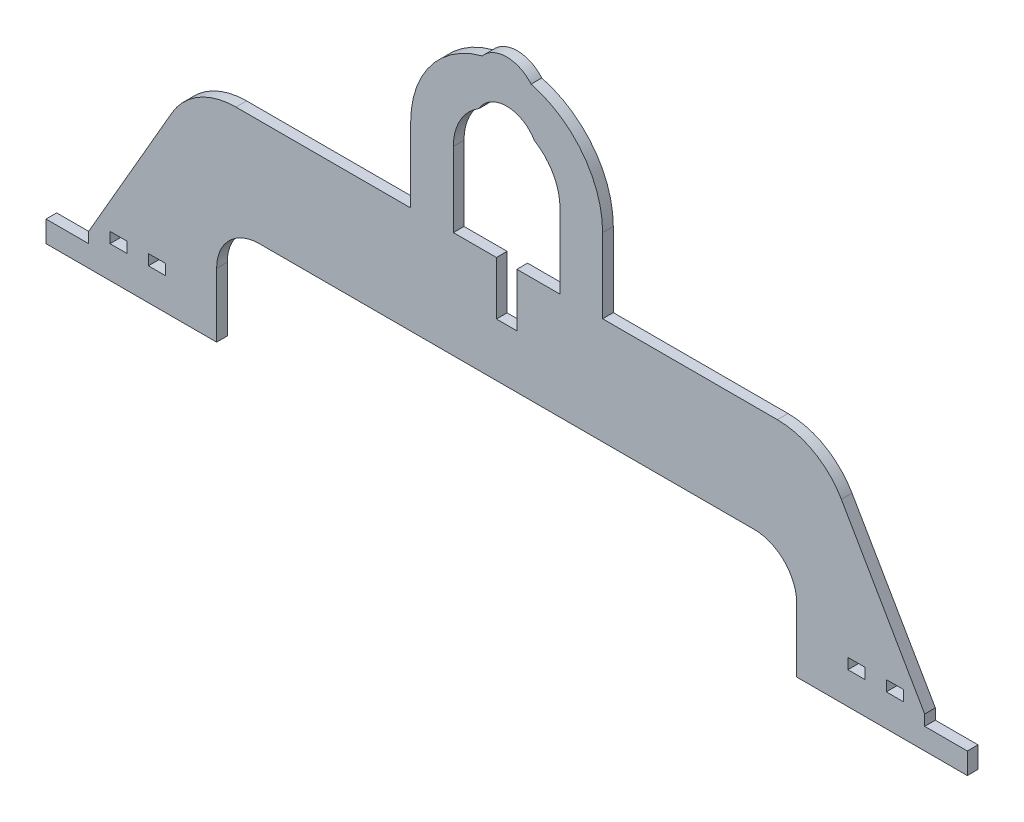
SolidWorks part; units mm, degrees
ref_plane "前视基准面" through (0, 0, 0) normal (0, 0, 1) x (1, 0, 0)
ref_plane "上视基准面" through (0, 0, 0) normal (0, 1, 0) x (1, 0, 0)
ref_plane "右视基准面" through (0, 0, 0) normal (1, 0, 0) x (0, 0, -1)
sketch "草图1" plane through (0, 0, 0) normal (0, 0, 1) x (1, 0, 0)
  line L12 (0, 256.6802) -> (0, -57.0056) construction
  line L13 (-216, 0) -> (-216, 10)
  line L14 (-216, 10) -> (-196, 10)
  line L15 (-196, 10) -> (-196, 15)
  line L17 (-196, 15) -> (-146.9252, 100)
  line L18 (-146.9252, 100) -> (146.9252, 100)
  line L20 (136, 50) -> (-136, 50)
  line L21 (-136, 50) -> (-136, 0)
  line L22 (-136, 0) -> (-216, 0)
  line L23 (136, 50) -> (136, 0)
  line L24 (136, 0) -> (216, 0)
  line L25 (216, 0) -> (216, 10)
  line L26 (216, 10) -> (196, 10)
  line L27 (196, 10) -> (196, 15)
  line L29 (196, 15) -> (146.9252, 100)
  point P5 (0, 0)
  point P8 (0, 256.6802)
  dimension "D1" = 10
  dimension "D2" = 5
  dimension "D3" = 20
  dimension "D4" = 50
  dimension "D5" = 392
  dimension "D6" = 80
  dimension "D7" = 100
  dimension "D8" = 60
extrude "凸台-拉伸1" add sketch "草图1" along normal blind 5
sketch "草图2" plane through (0, 0, 5) normal (0, 0, 1) x (1, 0, 0)
  line L0 (-146.9252, 100) -> (-126.9252, 100)
  line L1 (146.9252, 100) -> (-146.9252, 100) construction
  line L2 (-146.9252, 100) -> (-156.9252, 82.6795)
  line L3 (-146.9252, 100) -> (-196, 15) construction
  line L4 (0, 114.8473) -> (0, -48.9602) construction
  line L5 (146.9252, 100) -> (156.9252, 82.6795)
  line L6 (146.9252, 100) -> (126.9252, 100)
  arc A0 (-126.9252, 100) -> (-156.9252, 82.6795) centre (-126.9252, 65.359) ccw
  arc A1 (126.9252, 100) -> (156.9252, 82.6795) centre (126.9252, 65.359) cw
  dimension "D1" = 20
extrude "切除-拉伸1" cut sketch "草图2" against normal up to next
sketch "草图3" plane through (0, 0, 5) normal (0, 0, 1) x (1, 0, 0)
  line L0 (-116, 50) -> (-136, 50)
  line L1 (-136, 50) -> (136, 50) construction
  line L2 (-136, 50) -> (-136, 30)
  line L3 (-136, 0) -> (-136, 50) construction
  line L4 (0, 39.1826) -> (0, -70.8264) construction
  line L5 (136, 50) -> (136, 30)
  line L6 (116, 50) -> (136, 50)
  arc A0 (-116, 50) -> (-136, 30) centre (-116, 30) ccw
  arc A1 (116, 50) -> (136, 30) centre (116, 30) cw
  dimension "D1" = 20
extrude "凸台-拉伸2" add sketch "草图3" against normal up to surface (5 mm away) up to face at (0, 33.9623, 0)
sketch "草图4" plane through (0, 0, 5) normal (0, 0, 1) x (1, 0, 0)
  line L0 (126.9252, 100) -> (-126.9252, 100) construction
  line L1 (-4.8, 75) -> (4.8, 75)
  line L2 (-4.8, 75) -> (-4.8, 125)
  line L3 (-4.8, 125) -> (4.8, 125)
  line L4 (4.8, 75) -> (4.8, 125)
  line L5 (-4.8, 75) -> (4.8, 125) construction
  line L6 (-4.8, 125) -> (4.8, 75) construction
  point P0 (0, 100)
  dimension "D1" = 9.6
  dimension "D2" = 25
extrude "切除-拉伸2" cut sketch "草图4" against normal up to next
sketch "草图5" plane through (0, 0, 0) normal (0, 0, -1) x (-1, 0, 0)
  line L0 (45, 100) -> (45, 135)
  line L1 (4.8, 100) -> (126.9252, 100) construction
  line L2 (45, 100) -> (25, 100)
  line L3 (25, 100) -> (25, 135)
  line L4 (-25, 135) -> (-25, 100)
  line L5 (-126.9252, 100) -> (-4.8, 100) construction
  line L6 (-25, 100) -> (-45, 100)
  line L7 (-45, 100) -> (-45, 135)
  arc A0 (25, 135) -> (12.973, 156.3706) centre (0, 135) ccw
  arc A1 (45, 135) -> (11.4627, 178.5156) centre (0, 135) ccw
  arc A2 (12.973, 156.3706) -> (-12.973, 156.3706) centre (0, 148.8405) ccw
  arc A3 (11.4627, 178.5156) -> (-11.4627, 178.5156) centre (0, 168.8405) ccw
  arc A4 (-12.973, 156.3706) -> (-25, 135) centre (0, 135) ccw
  arc A5 (-11.4627, 178.5156) -> (-45, 135) centre (0, 135) ccw
  point P20 (0, 0)
  point P21 (0, 0)
  point P22 (0, 157.9139)
  point P23 (0, 156.6723)
  point P24 (0, 151.4636)
  point P25 (0, 144.4888)
  point P26 (0, 147.7392)
  point P27 (0, 168.331)
  point P28 (0, 148.1426)
  point P29 (0, 148.8405)
  dimension "D1" = 20
  dimension "D4" = 15
  dimension "D5" = 15
  dimension "D6" = 20
  dimension "D2" = 50
  dimension "D3" = 35
extrude "凸台-拉伸3" add sketch "草图5" against normal blind 5
sketch "草图6" plane through (0, 0, 5) normal (0, 0, 1) x (1, 0, 0)
  line L0 (-196, 10) -> (-216, 10) construction
  line L1 (-186, 15) -> (-178, 15)
  line L2 (-186, 15) -> (-186, 20)
  line L3 (-186, 20) -> (-178, 20)
  line L4 (-178, 15) -> (-178, 20)
  line L5 (-186, 15) -> (-178, 20) construction
  line L6 (-186, 20) -> (-178, 15) construction
  line L7 (-168, 15) -> (-160, 15)
  line L8 (-168, 15) -> (-168, 20)
  line L9 (-168, 20) -> (-160, 20)
  line L10 (-160, 15) -> (-160, 20)
  line L11 (-168, 15) -> (-160, 20) construction
  line L12 (-168, 20) -> (-160, 15) construction
  line L13 (0, 29.1114) -> (0, -52.1724) construction
  line L14 (186, 20) -> (178, 20)
  line L15 (178, 15) -> (178, 20)
  line L16 (186, 15) -> (178, 15)
  line L17 (186, 15) -> (186, 20)
  line L18 (168, 20) -> (160, 20)
  line L19 (160, 15) -> (160, 20)
  line L20 (168, 15) -> (160, 15)
  line L21 (168, 15) -> (168, 20)
  point P4 (-182, 17.5)
  point P9 (-164, 17.5)
  dimension "D1" = 5
  dimension "D2" = 5
  dimension "D3" = 8
  dimension "D4" = 8
  dimension "D5" = 5
  dimension "D6" = 10
  dimension "D7" = 10
extrude "切除-拉伸3" cut sketch "草图6" against normal up to next
